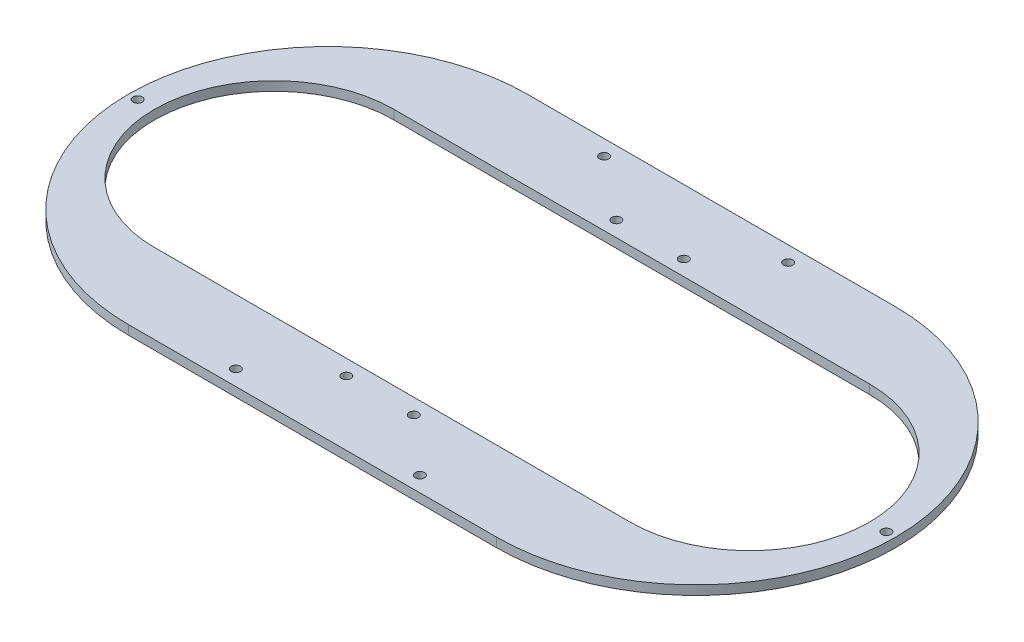
SolidWorks part; units mm, degrees
ref_plane "前视基准面" through (0, 0, 0) normal (0, 0, 1) x (1, 0, 0)
ref_plane "上视基准面" through (0, 0, 0) normal (0, 1, 0) x (1, 0, 0)
ref_plane "右视基准面" through (0, 0, 0) normal (1, 0, 0) x (0, 0, -1)
sketch "草图1" plane through (0, 0, 0) normal (0, 1, 0) x (1, 0, 0)
  line L0 (0, 0) -> (0, 89.0672) construction
  line L1 (-60, 0) -> (60, 0) construction
  line L2 (-60, 70) -> (60, 70) construction
  line L3 (-60, -70) -> (60, -70) construction
  line L4 (-90, 51.9615) -> (-60, 0) construction
  line L5 (-90, -51.9615) -> (-60, 0) construction
  line L6 (90, -51.9615) -> (60, 0) construction
  line L7 (90, 51.9615) -> (60, 0) construction
  line L8 (0, 0) -> (76.6344, 0) construction
  line L9 (-49.5811, 59.0885) -> (-60, 0) construction
  line L10 (-116.3816, -20.5212) -> (-60, 0) construction
  line L11 (-14.0373, -38.5673) -> (-60, 0) construction
  line L12 (-60, 65) -> (60, 65)
  line L13 (-60, -65) -> (60, -65)
  arc A2 (-60, 70) -> (-60, -70) centre (-60, 0) ccw construction
  arc A3 (60, -70) -> (60, 70) centre (60, 0) ccw construction
  circle A4 centre (0, 0) radius 1.5 construction
  circle A5 centre (-90, 51.9615) radius 1.5 construction
  circle A6 centre (-90, -51.9615) radius 1.5 construction
  circle A7 centre (90, -51.9615) radius 1.5 construction
  circle A8 centre (90, 51.9615) radius 1.5 construction
  circle A9 centre (0, 0) radius 1.5 construction
  circle A10 centre (-122, 0) radius 1.5
  circle A11 centre (122, 0) radius 1.5
  circle A12 centre (-30, 60) radius 1.5
  circle A13 centre (30, 60) radius 1.5
  circle A14 centre (30, -60) radius 1.5
  circle A15 centre (-30, -60) radius 1.5
  arc A22 (60, -65) -> (60, 65) centre (60, 0) ccw
  arc A23 (-60, 65) -> (-60, -65) centre (-60, 0) ccw
  point P7 (0, 0)
  dimension "D3" = 5
  dimension "D4" = 3
  dimension "D7" = 3
  dimension "D9" = 3
  dimension "D10" = 60
  dimension "D12" = 3
  dimension "D13" = 62
  dimension "D14" = 62
  dimension "D15" = 3
  dimension "D16" = 3
  dimension "D18" = 60
  dimension "D8" = 120
  dimension "D11" = 120
  dimension "D17" = 30
  dimension "D20" = 60
  dimension "D21" = 80
  dimension "D24" = 120
  dimension "D26" = 60
  dimension "D27" = 120
extrude "凸台-拉伸2" add sketch "草图1" along normal blind 3
sketch "草图2" plane through (0, 3, 0) normal (0, 1, 0) x (1, 0, 0)
  circle A0 centre (-10, 44) radius 1.5
  circle A1 centre (12, 44) radius 1.5
  circle A2 centre (-10, -44) radius 1.5
  circle A3 centre (12, -44) radius 1.5
extrude "切除-拉伸1" cut sketch "草图2" against normal blind 10
sketch "草图3" plane through (0, 3, 0) normal (0, 1, 0) x (1, 0, 0)
  line L0 (-77.5, 0) -> (77.5, 0) construction
  line L1 (-77.5, 39) -> (77.5, 39)
  line L2 (-77.5, -39) -> (77.5, -39)
  arc A0 (-77.5, 39) -> (-77.5, -39) centre (-77.5, 0) ccw
  arc A1 (77.5, -39) -> (77.5, 39) centre (77.5, 0) ccw
  point P3 (0, 0)
  point P8 (0, 0)
  dimension "D1" = 39
  dimension "D2" = 155
extrude "切除-拉伸2" cut sketch "草图3" against normal blind 10
